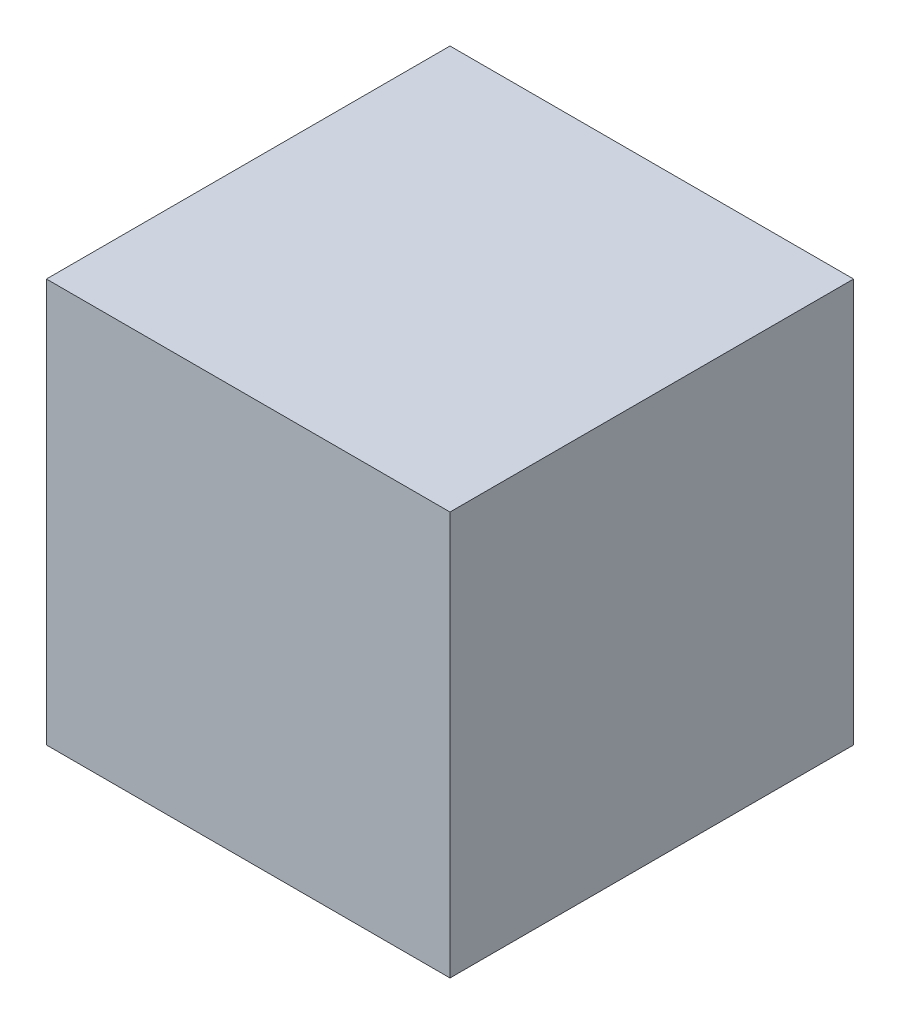
SolidWorks part; units mm, degrees
ref_plane "Front Plane" through (0, 0, 0) normal (0, 0, 1) x (1, 0, 0)
ref_plane "Top Plane" through (0, 0, 0) normal (0, 1, 0) x (1, 0, 0)
ref_plane "Right Plane" through (0, 0, 0) normal (1, 0, 0) x (0, 0, -1)
sketch "Sketch1" plane through (0, 0, 0) normal (0, 1, 0) x (1, 0, 0)
  line L1 (12.7, -12.7) -> (-12.7, -12.7)
  line L2 (12.7, -12.7) -> (12.7, 12.7)
  line L3 (12.7, 12.7) -> (-12.7, 12.7)
  line L4 (-12.7, -12.7) -> (-12.7, 12.7)
  line L5 (12.7, -12.7) -> (-12.7, 12.7) construction
  line L6 (12.7, 12.7) -> (-12.7, -12.7) construction
  point P0 (0, 0)
  dimension "D1" = 25.4
  dimension "D2" = 25.4
extrude "Boss-Extrude1" add sketch "Sketch1" along normal blind 25.4
